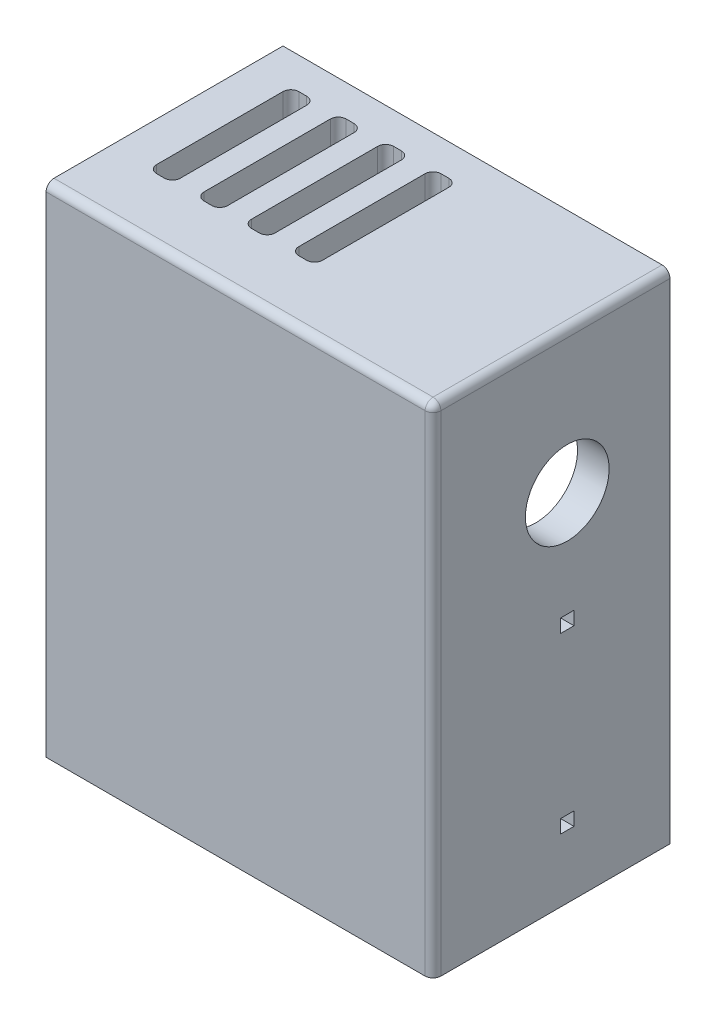
SolidWorks part; units mm, degrees
ref_plane "Спереди" through (0, 0, 0) normal (0, 0, 1) x (1, 0, 0)
ref_plane "Сверху" through (0, 0, 0) normal (0, 1, 0) x (1, 0, 0)
ref_plane "Справа" through (0, 0, 0) normal (1, 0, 0) x (0, 0, -1)
sketch "Эскиз1" plane through (0, 0, 0) normal (0, 0, 1) x (1, 0, 0)
  line L1 (-22.2955, 27.2045) -> (26.7045, 27.2045)
  line L2 (-22.2955, 27.2045) -> (-22.2955, -35.7955)
  line L3 (-22.2955, -35.7955) -> (26.7045, -35.7955)
  line L4 (26.7045, 27.2045) -> (26.7045, -35.7955)
  dimension "D1" = 63
  dimension "D2" = 49
extrude "Бобышка-Вытянуть1" add sketch "Эскиз1" along normal blind 4
sketch "Эскиз2" plane through (0, 0, 0) normal (0, 0, -1) x (-1, 0, 0)
  line L0 (-26.7045, -35.7955) -> (-26.7045, 27.2045) construction
  line L1 (22.2955, 27.2045) -> (-26.7045, 27.2045)
  line L2 (22.2955, 27.2045) -> (22.2955, 23.2045)
  line L3 (22.2955, 23.2045) -> (-26.7045, 23.2045)
  line L4 (-26.7045, 27.2045) -> (-26.7045, 23.2045)
  line L6 (-26.7045, -35.7955) -> (-22.7045, -35.7955)
  line L7 (-26.7045, -35.7955) -> (-26.7045, 27.2045)
  line L8 (-26.7045, 27.2045) -> (-22.7045, 27.2045)
  line L9 (-22.7045, -35.7955) -> (-22.7045, 27.2045)
  line M7 (22.2955, -35.7955) -> (22.2955, 27.2045)
  line M8 (22.2955, 27.2045) -> (-26.7045, 27.2045)
  line M9 (-26.7045, 27.2045) -> (-26.7045, -35.7955)
  line M10 (-26.7045, -35.7955) -> (22.2955, -35.7955)
  dimension "D1" = 4
  dimension "D2" = 4
extrude "Бобышка-Вытянуть2" add sketch "Эскиз2" along normal blind 26 contours L9 L3 M7 M8 | L9 L3 M10 M9 | L3 L9 L1 M9
sketch "Эскиз3" plane through (0, 0, 0) normal (0, 0, -1) x (-1, 0, 0)
  line L0 (-22.7045, -35.7955) -> (-22.7045, 23.2045) construction
  line L1 (-22.7045, 23.2045) -> (-8.7045, 23.2045)
  line L2 (-22.7045, 23.2045) -> (-22.7045, 15.2045)
  line L3 (-22.7045, 15.2045) -> (-8.7045, 15.2045)
  line L4 (-8.7045, 23.2045) -> (-8.7045, 15.2045)
  line L5 (-22.7045, -27.7955) -> (7.2955, -27.7955)
  line L6 (-22.7045, -27.7955) -> (-22.7045, -19.7955)
  line L7 (-22.7045, -19.7955) -> (7.2955, -19.7955)
  line L8 (7.2955, -27.7955) -> (7.2955, -19.7955)
  line L9 (22.2955, 23.2045) -> (-22.7045, 23.2045) construction
  point P5 (-22.7045, 19.2045)
  dimension "D1" = 8
  dimension "D2" = 14
  dimension "D3" = 51
  dimension "D4" = 8
  dimension "D5" = 30
extrude "Бобышка-Вытянуть3" add sketch "Эскиз3" along normal blind 7.2
sketch "Эскиз5" plane through (22.7045, 0, 0) normal (-1, 0, 0) x (0, 0, 1)
  line L0 (-26, 23.2045) -> (-7.2, 23.2045) construction
  line L1 (-26, -35.7955) -> (-26, 23.2045) construction
  circle A0 centre (-13, 9.2045) radius 5.3
  dimension "D2" = 10.6
  dimension "D1" = 14
  dimension "D3" = 13
extrude "Вырез-Вытянуть1" cut sketch "Эскиз5" against normal blind 4
sketch "Эскиз6" plane through (26.7045, 0, 0) normal (1, 0, 0) x (0, 0, -1)
  line L1 (12.15, -4.0955) -> (13.85, -4.0955)
  line L2 (12.15, -4.0955) -> (12.15, -5.7955)
  line L3 (12.15, -5.7955) -> (13.85, -5.7955)
  line L4 (13.85, -4.0955) -> (13.85, -5.7955)
  line L5 (12.15, -26.0955) -> (13.85, -26.0955)
  line L6 (12.15, -26.0955) -> (12.15, -27.7955)
  line L7 (12.15, -27.7955) -> (13.85, -27.7955)
  line L8 (13.85, -26.0955) -> (13.85, -27.7955)
  line L11 (-4, -35.7955) -> (-4, 27.2045) construction
  line L12 (-4, -35.7955) -> (26, -35.7955) construction
  point P8 (13, -5.7955)
  point P9 (12.15, -4.9455)
  dimension "D1" = 1.7
  dimension "D2" = 1.7
  dimension "D3" = 1.7
  dimension "D4" = 1.7
  dimension "D5" = 0
  dimension "D6" = 16.15
  dimension "D7" = 8
  dimension "D8" = 30
sketch "Эскиз7" plane through (-22.2955, 0, 0) normal (-1, 0, 0) x (0, 0, 1)
  line L1 (2.6, 25.8045) -> (0.9, 25.8045)
  line L2 (2.6, 25.8045) -> (2.6, 24.1045)
  line L3 (2.6, 24.1045) -> (0.9, 24.1045)
  line L4 (0.9, 25.8045) -> (0.9, 24.1045)
extrude "Вырез-Вытянуть3" cut sketch "Эскиз7" against normal blind 6
sketch "Эскиз8" plane through (0, -35.7955, 0) normal (0, -1, 0) x (1, 0, 0)
  line L1 (23.6045, 0.9) -> (25.3045, 0.9)
  line L2 (23.6045, 0.9) -> (23.6045, 2.6)
  line L3 (23.6045, 2.6) -> (25.3045, 2.6)
  line L4 (25.3045, 0.9) -> (25.3045, 2.6)
extrude "Вырез-Вытянуть4" cut sketch "Эскиз8" against normal blind 6
sketch "Эскиз9" plane through (0, 0, -26) normal (0, 0, -1) x (-1, 0, 0)
  line L1 (-23.6045, 24.1045) -> (-25.3045, 24.1045)
  line L2 (-23.6045, 24.1045) -> (-23.6045, 25.8045)
  line L3 (-23.6045, 25.8045) -> (-25.3045, 25.8045)
  line L4 (-25.3045, 24.1045) -> (-25.3045, 25.8045)
extrude "Вырез-Вытянуть5" cut sketch "Эскиз9" against normal blind 6
fillet "Скругление1" radius 1 3 edges at (26.7045, -4.2955, 4) (26.7045, 27.2045, -11) (2.2045, 27.2045, 4)
extrude "Вырез-Вытянуть7" cut sketch "Эскиз6" against normal blind 5
sketch "Эскиз10" plane through (22.7045, 0, 0) normal (-1, 0, 0) x (0, 0, 1)
  line L0 (0, -19.7955) -> (0, 15.2045) construction
  line L1 (0, -2.0955) -> (-15, -2.0955)
  line L2 (0, -2.0955) -> (0, -29.7955)
  line L3 (0, -29.7955) -> (-15, -29.7955)
  line L4 (-15, -2.0955) -> (-15, -29.7955)
  line L5 (-13.85, -5.7955) -> (-13.85, -4.0955) construction
  line L6 (-13.85, -4.0955) -> (-12.15, -4.0955) construction
  line L7 (-12.15, -27.7955) -> (-13.85, -27.7955) construction
  point P8 (-13.85, -4.9455)
  dimension "D1" = 1.15
  dimension "D2" = 2
  dimension "D3" = 2
extrude "Бобышка-Вытянуть4" add sketch "Эскиз10" along normal blind 2
sketch "Эскиз11" plane through (0, 27.2045, 0) normal (0, 1, 0) x (1, 0, 0)
  line L0 (26.7045, 26) -> (26.7045, -3) construction
  line L1 (2.7045, 4) -> (1.7045, 4)
  line L2 (3.7045, 5) -> (3.7045, 21)
  line L3 (2.7045, 22) -> (1.7045, 22)
  line L4 (0.7045, 5) -> (0.7045, 21)
  line L5 (-3.2955, 4) -> (-4.2955, 4)
  line L6 (-2.2955, 5) -> (-2.2955, 21)
  line L7 (-3.2955, 22) -> (-4.2955, 22)
  line L8 (-5.2955, 5) -> (-5.2955, 21)
  line L9 (-9.2955, 4) -> (-10.2955, 4)
  line L10 (-8.2955, 5) -> (-8.2955, 21)
  line L11 (-9.2955, 22) -> (-10.2955, 22)
  line L12 (-11.2955, 5) -> (-11.2955, 21)
  line L13 (-15.2955, 4) -> (-16.2955, 4)
  line L14 (-14.2955, 5) -> (-14.2955, 21)
  line L15 (-15.2955, 22) -> (-16.2955, 22)
  line L16 (-17.2955, 5) -> (-17.2955, 21)
  line L17 (25.7045, -4) -> (-22.2955, -4) construction
  arc A0 (3.7045, 21) -> (2.7045, 22) centre (2.7045, 21) ccw
  arc A1 (1.7045, 22) -> (0.7045, 21) centre (1.7045, 21) ccw
  arc A2 (-2.2955, 21) -> (-3.2955, 22) centre (-3.2955, 21) ccw
  arc A3 (-4.2955, 22) -> (-5.2955, 21) centre (-4.2955, 21) ccw
  arc A4 (-8.2955, 21) -> (-9.2955, 22) centre (-9.2955, 21) ccw
  arc A5 (-10.2955, 22) -> (-11.2955, 21) centre (-10.2955, 21) ccw
  arc A6 (-14.2955, 21) -> (-15.2955, 22) centre (-15.2955, 21) ccw
  arc A7 (-16.2955, 22) -> (-17.2955, 21) centre (-16.2955, 21) ccw
  arc A8 (-16.2955, 4) -> (-17.2955, 5) centre (-16.2955, 5) cw
  arc A9 (-15.2955, 4) -> (-14.2955, 5) centre (-15.2955, 5) ccw
  arc A10 (-10.2955, 4) -> (-11.2955, 5) centre (-10.2955, 5) cw
  arc A11 (-9.2955, 4) -> (-8.2955, 5) centre (-9.2955, 5) ccw
  arc A12 (-4.2955, 4) -> (-5.2955, 5) centre (-4.2955, 5) cw
  arc A13 (-3.2955, 4) -> (-2.2955, 5) centre (-3.2955, 5) ccw
  arc A14 (1.7045, 4) -> (0.7045, 5) centre (1.7045, 5) cw
  arc A15 (2.7045, 4) -> (3.7045, 5) centre (2.7045, 5) ccw
  point P50 (2.2045, 4)
  dimension "D1" = 1
  dimension "D2" = 3
  dimension "D3" = 3
  dimension "D4" = 3
  dimension "D5" = 3
  dimension "D6" = 23
  dimension "D7" = 3
  dimension "D8" = 3
  dimension "D9" = 3
  dimension "D10" = 0
  dimension "D11" = 0
  dimension "D12" = 0
  dimension "D13" = 18
  dimension "D14" = 18
  dimension "D15" = 18
  dimension "D16" = 18
  dimension "D17" = 8
extrude "Вырез-Вытянуть8" cut sketch "Эскиз11" against normal blind 13
sketch "Эскиз12" plane through (0, 0, -7.2) normal (0, 0, -1) x (-1, 0, 0)
  line L0 (-8.7045, 23.2045) -> (-22.7045, 23.2045) construction
  line L1 (-14.5045, 22.1045) -> (-12.8045, 22.1045)
  line L2 (-14.5045, 22.1045) -> (-14.5045, 20.4045)
  line L3 (-14.5045, 20.4045) -> (-12.8045, 20.4045)
  line L4 (-12.8045, 22.1045) -> (-12.8045, 20.4045)
  line L5 (-14.5045, -23.2455) -> (-12.8045, -23.2455)
  line L6 (-14.5045, -23.2455) -> (-14.5045, -24.9455)
  line L7 (-14.5045, -24.9455) -> (-12.8045, -24.9455)
  line L8 (-12.8045, -23.2455) -> (-12.8045, -24.9455)
  line L9 (-22.7045, 23.2045) -> (-22.7045, 15.2045) construction
  point P8 (-13.6545, 20.4045)
  point P9 (-12.8045, 21.2545)
  point P12 (-12.8045, -24.0955)
  point P13 (-13.6545, 22.1045)
  dimension "D1" = 1.7
  dimension "D2" = 1.7
  dimension "D3" = 1.7
  dimension "D4" = 1.7
  dimension "D5" = 0
  dimension "D6" = 1.95
  dimension "D7" = 45.35
  dimension "D8" = 9.05
extrude "Вырез-Вытянуть9" cut sketch "Эскиз12" against normal blind 5
